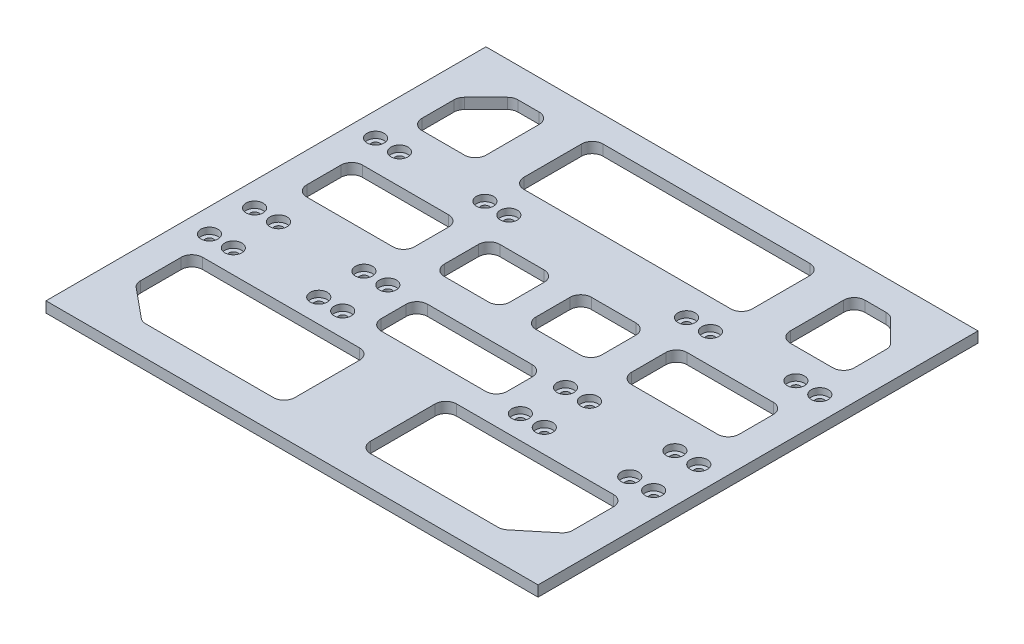
SolidWorks part; units mm, degrees
material "Custom Plastic"
ref_plane "Front Plane" through (0, 0, 0) normal (0, 0, 1) x (1, 0, 0)
ref_plane "Top Plane" through (0, 0, 0) normal (0, 1, 0) x (1, 0, 0)
ref_plane "Right Plane" through (0, 0, 0) normal (1, 0, 0) x (0, 0, -1)
sketch "Sketch1" plane through (0, 0, 0) normal (0, 1, 0) x (1, 0, 0)
  line L1 (-57.5, -51.5) -> (57.5, -51.5)
  line L2 (-57.5, -51.5) -> (-57.5, 51.5)
  line L3 (-57.5, 51.5) -> (57.5, 51.5)
  line L4 (57.5, -51.5) -> (57.5, 51.5)
  line L5 (-57.5, -51.5) -> (57.5, 51.5) construction
  line L6 (-57.5, 51.5) -> (57.5, -51.5) construction
  point P0 (0, 0)
  dimension "D1" = 115
  dimension "D2" = 103
extrude "Boss-Extrude1" add sketch "Sketch1" along normal blind 2.5
sketch "Sketch2" plane through (0, 0, 0) normal (0, -1, 0) x (1, 0, 0)
  line L0 (-57.5, 51.5) -> (57.5, 51.5) construction
  line L1 (-57.5, -51.5) -> (-57.5, 51.5) construction
  line L2 (0, 51.5) -> (0, -51.5) construction
  line L3 (57.5, -51.5) -> (-57.5, -51.5) construction
  line L4 (-46.4, 51.5) -> (-46.4, -51.5) construction
  circle A0 centre (-52, -20.06) radius 1
  circle A1 centre (-52, 8.27) radius 1
  circle A2 centre (-52, 18.84) radius 1
  circle A3 centre (52, -20.06) radius 1
  circle A4 centre (52, 8.27) radius 1
  circle A5 centre (52, 18.84) radius 1
  circle A6 centre (-46.4, 18.84) radius 1
  circle A7 centre (-46.4, -20.06) radius 1
  circle A8 centre (-46.4, 8.27) radius 1
  circle A9 centre (46.4, -20.06) radius 1
  circle A10 centre (46.4, 8.27) radius 1
  circle A11 centre (46.4, 18.84) radius 1
  dimension "D7" = 2
  dimension "D8" = 2
  dimension "D9" = 2
  dimension "D12" = 2
  dimension "D14" = 2
  dimension "D15" = 43.23
  dimension "D16" = 2
  dimension "D1" = 32.66
  dimension "D2" = 43.23
  dimension "D3" = 71.56
  dimension "D4" = 5.5
  dimension "D5" = 5.5
  dimension "D6" = 5.5
  dimension "D10" = 11.1
  dimension "D11" = 32.66
  dimension "D13" = 71.56
extrude "Cut-Extrude1" cut sketch "Sketch2" against normal blind 10
sketch "Sketch3" plane through (-57.5, 0, 0) normal (-1, 0, 0) x (0, 0, 1)
  line L8 (-51.5, 0) -> (51.5, 0)
  line L9 (51.5, 0) -> (51.5, 2.5)
  line L10 (51.5, 2.5) -> (-51.5, 2.5)
  line L11 (-51.5, 2.5) -> (-51.5, 0)
  line L12 (-51.5, 0) -> (51.5, 0)
  line L13 (51.5, 0) -> (51.5, 2.5)
  line L14 (51.5, 2.5) -> (-51.5, 2.5)
  line L15 (-51.5, 2.5) -> (-51.5, 0)
  dimension "D1" = 0
extrude "Boss-Extrude2" add sketch "Sketch3" along normal blind 0.1
sketch "Sketch4" plane through (57.5, 0, 0) normal (1, 0, 0) x (0, 0, -1)
  line L4 (-51.5, 0) -> (51.5, 0)
  line L5 (51.5, 0) -> (51.5, 2.5)
  line L6 (51.5, 2.5) -> (-51.5, 2.5)
  line L7 (-51.5, 2.5) -> (-51.5, 0)
  line L8 (-51.5, 0) -> (51.5, 0)
  line L9 (51.5, 0) -> (51.5, 2.5)
  line L10 (51.5, 2.5) -> (-51.5, 2.5)
  line L11 (-51.5, 2.5) -> (-51.5, 0)
  dimension "D1" = 0
extrude "Boss-Extrude3" add sketch "Sketch4" along normal blind 0.1
sketch "Sketch5" plane through (0, 2.5, 0) normal (0, 1, 0) x (1, 0, 0)
  line L0 (-52, 20.06) -> (52, 20.06) construction
  line L1 (-52, -8.27) -> (52, -8.27) construction
  line L2 (-52, -18.84) -> (52, -18.84) construction
  line L3 (0, 51.5) -> (0, -51.5) construction
  line L4 (57.6, 51.5) -> (-57.6, 51.5) construction
  line L5 (-57.6, -51.5) -> (57.6, -51.5) construction
  circle A0 centre (-26.4, 20.06) radius 1
  circle A1 centre (-26.4, -8.27) radius 1
  circle A2 centre (-26.4, -18.84) radius 1
  circle A3 centre (-20.8, 20.06) radius 1
  circle A4 centre (-20.8, -8.27) radius 1
  circle A5 centre (-20.8, -18.84) radius 1
  circle A6 centre (26.4, -18.84) radius 1
  circle A7 centre (20.8, -18.84) radius 1
  circle A8 centre (26.4, -8.27) radius 1
  circle A9 centre (20.8, -8.27) radius 1
  circle A10 centre (26.4, 20.06) radius 1
  circle A11 centre (20.8, 20.06) radius 1
  dimension "D4" = 2
  dimension "D5" = 2
  dimension "D6" = 2
  dimension "D7" = 2
  dimension "D8" = 2
  dimension "D9" = 2
  dimension "D1" = 31.2
  dimension "D2" = 31.2
  dimension "D3" = 31.2
  dimension "D10" = 5.6
  dimension "D11" = 5.6
  dimension "D12" = 5.6
extrude "Cut-Extrude2" cut sketch "Sketch5" against normal blind 10
sketch "Sketch6" plane through (0, 2.5, 0) normal (0, 1, 0) x (1, 0, 0)
  line L0 (-44.8762, 43.7678) -> (-49.8678, 38.7762)
  line L1 (-50.6, 37.0084) -> (-50.6, 29.5256)
  line L2 (-48.1, 27.0256) -> (-38.1257, 27.0256)
  line L3 (-35.6257, 29.5256) -> (-35.6257, 42)
  line L4 (-38.1257, 44.5) -> (-43.1084, 44.5)
  line L5 (57.6, 51.5) -> (-57.6, 51.5) construction
  line L6 (0, 64.7841) -> (0, -71.4614) construction
  line L7 (-24.2114, 45.5) -> (24.2114, 45.5)
  line L8 (-26.7114, 43) -> (-26.7114, 29.5256)
  line L9 (-24.2114, 27.0256) -> (24.2114, 27.0256)
  line L10 (26.7114, 43) -> (26.7114, 29.5256)
  line L11 (-49.6888, -38.3001) -> (-42.8486, -43.9302)
  line L12 (-48.1, 0.0564) -> (-27.9271, 0.0564)
  line L13 (-50.6, 2.5564) -> (-50.6, 10.569)
  line L14 (-48.1, 13.069) -> (-27.9271, 13.069)
  line L15 (-25.4271, 2.5564) -> (-25.4271, 10.569)
  line L16 (-50.6, 0.0564) -> (-25.4271, 13.069) construction
  line L17 (-50.6, 13.069) -> (-25.4271, 0.0564) construction
  line L18 (-15.9179, 0.0564) -> (-5.5337, 0.0564)
  line L19 (-18.4179, 2.5564) -> (-18.4179, 10.569)
  line L20 (-15.9179, 13.069) -> (-5.5337, 13.069)
  line L21 (-3.0337, 2.5564) -> (-3.0337, 10.569)
  line L22 (-18.4179, 0.0564) -> (-3.0337, 13.069) construction
  line L23 (-18.4179, 13.069) -> (-3.0337, 0.0564) construction
  line L24 (-41.2598, -44.5) -> (-11.3488, -44.5)
  line L25 (-50.6, -36.3699) -> (-50.6, -26.8363)
  line L26 (-48.1, -24.3363) -> (-11.3488, -24.3363)
  line L27 (-8.8488, -42) -> (-8.8488, -26.8363)
  line L28 (-47.0786, -40.4486) -> (-8.8488, -24.3363) construction
  line L29 (-50.6, -24.3363) -> (-8.8488, -44.5) construction
  line L30 (-57.6, -51.5) -> (-57.6, 51.5) construction
  line L32 (-57.6, -51.5) -> (57.6, -51.5) construction
  line L33 (41.2598, -44.5) -> (11.3488, -44.5)
  line L34 (-12.2501, -18.3965) -> (12.2501, -18.3965)
  line L35 (-14.7501, -15.8965) -> (-14.7501, -10.0236)
  line L36 (-12.2501, -7.5236) -> (12.2501, -7.5236)
  line L37 (14.7501, -15.8965) -> (14.7501, -10.0236)
  line L38 (-14.7501, -18.3965) -> (14.7501, -7.5236) construction
  line L39 (-14.7501, -7.5236) -> (14.7501, -18.3965) construction
  line L40 (8.8488, -42) -> (8.8488, -26.8363)
  line L41 (48.1, -24.3363) -> (11.3488, -24.3363)
  line L42 (50.6, -36.3699) -> (50.6, -26.8363)
  line L43 (49.6888, -38.3001) -> (42.8486, -43.9302)
  line L44 (3.0337, 2.5564) -> (3.0337, 10.569)
  line L45 (15.9179, 13.069) -> (5.5337, 13.069)
  line L46 (18.4179, 2.5564) -> (18.4179, 10.569)
  line L47 (15.9179, 0.0564) -> (5.5337, 0.0564)
  line L48 (48.1, 0.0564) -> (27.9271, 0.0564)
  line L49 (50.6, 2.5564) -> (50.6, 10.569)
  line L50 (48.1, 13.069) -> (27.9271, 13.069)
  line L51 (25.4271, 2.5564) -> (25.4271, 10.569)
  line L52 (48.1, 27.0256) -> (38.1257, 27.0256)
  line L53 (50.6, 37.0084) -> (50.6, 29.5256)
  line L54 (44.8762, 43.7678) -> (49.8678, 38.7762)
  line L55 (38.1257, 44.5) -> (43.1084, 44.5)
  line L56 (35.6257, 29.5256) -> (35.6257, 42)
  arc A0 (-49.8678, 38.7762) -> (-50.6, 37.0084) centre (-48.1, 37.0084) ccw
  arc A1 (-44.8762, 43.7678) -> (-43.1084, 44.5) centre (-43.1084, 42) cw
  arc A2 (-42.8486, -43.9302) -> (-41.2598, -44.5) centre (-41.2598, -42) ccw
  arc A3 (-49.6888, -38.3001) -> (-50.6, -36.3699) centre (-48.1, -36.3699) cw
  arc A4 (-50.6, -26.8363) -> (-48.1, -24.3363) centre (-48.1, -26.8363) cw
  arc A5 (-11.3488, -44.5) -> (-8.8488, -42) centre (-11.3488, -42) ccw
  arc A6 (-11.3488, -24.3363) -> (-8.8488, -26.8363) centre (-11.3488, -26.8363) cw
  arc A7 (12.2501, -7.5236) -> (14.7501, -10.0236) centre (12.2501, -10.0236) cw
  arc A8 (12.2501, -18.3965) -> (14.7501, -15.8965) centre (12.2501, -15.8965) ccw
  arc A9 (-12.2501, -18.3965) -> (-14.7501, -15.8965) centre (-12.2501, -15.8965) cw
  arc A10 (-14.7501, -10.0236) -> (-12.2501, -7.5236) centre (-12.2501, -10.0236) cw
  arc A11 (-27.9271, 13.069) -> (-25.4271, 10.569) centre (-27.9271, 10.569) cw
  arc A12 (-27.9271, 0.0564) -> (-25.4271, 2.5564) centre (-27.9271, 2.5564) ccw
  arc A13 (-48.1, 0.0564) -> (-50.6, 2.5564) centre (-48.1, 2.5564) cw
  arc A14 (-50.6, 10.569) -> (-48.1, 13.069) centre (-48.1, 10.569) cw
  arc A15 (24.2114, 27.0256) -> (26.7114, 29.5256) centre (24.2114, 29.5256) ccw
  arc A16 (24.2114, 45.5) -> (26.7114, 43) centre (24.2114, 43) cw
  arc A17 (-5.5337, 13.069) -> (-3.0337, 10.569) centre (-5.5337, 10.569) cw
  arc A18 (-5.5337, 0.0564) -> (-3.0337, 2.5564) centre (-5.5337, 2.5564) ccw
  arc A19 (-15.9179, 0.0564) -> (-18.4179, 2.5564) centre (-15.9179, 2.5564) cw
  arc A20 (-18.4179, 10.569) -> (-15.9179, 13.069) centre (-15.9179, 10.569) cw
  arc A21 (-24.2114, 45.5) -> (-26.7114, 43) centre (-24.2114, 43) ccw
  arc A22 (-26.7114, 29.5256) -> (-24.2114, 27.0256) centre (-24.2114, 29.5256) ccw
  arc A23 (-38.1257, 27.0256) -> (-35.6257, 29.5256) centre (-38.1257, 29.5256) ccw
  arc A24 (-35.6257, 42) -> (-38.1257, 44.5) centre (-38.1257, 42) ccw
  arc A25 (-50.6, 29.5256) -> (-48.1, 27.0256) centre (-48.1, 29.5256) ccw
  arc A26 (42.8486, -43.9302) -> (41.2598, -44.5) centre (41.2598, -42) cw
  arc A27 (11.3488, -44.5) -> (8.8488, -42) centre (11.3488, -42) cw
  arc A28 (11.3488, -24.3363) -> (8.8488, -26.8363) centre (11.3488, -26.8363) ccw
  arc A29 (50.6, -26.8363) -> (48.1, -24.3363) centre (48.1, -26.8363) ccw
  arc A30 (49.6888, -38.3001) -> (50.6, -36.3699) centre (48.1, -36.3699) ccw
  arc A31 (5.5337, 0.0564) -> (3.0337, 2.5564) centre (5.5337, 2.5564) cw
  arc A32 (5.5337, 13.069) -> (3.0337, 10.569) centre (5.5337, 10.569) ccw
  arc A33 (18.4179, 10.569) -> (15.9179, 13.069) centre (15.9179, 10.569) ccw
  arc A34 (15.9179, 0.0564) -> (18.4179, 2.5564) centre (15.9179, 2.5564) ccw
  arc A35 (27.9271, 13.069) -> (25.4271, 10.569) centre (27.9271, 10.569) ccw
  arc A36 (27.9271, 0.0564) -> (25.4271, 2.5564) centre (27.9271, 2.5564) cw
  arc A37 (48.1, 0.0564) -> (50.6, 2.5564) centre (48.1, 2.5564) ccw
  arc A38 (50.6, 10.569) -> (48.1, 13.069) centre (48.1, 10.569) ccw
  arc A39 (38.1257, 27.0256) -> (35.6257, 29.5256) centre (38.1257, 29.5256) cw
  arc A40 (50.6, 29.5256) -> (48.1, 27.0256) centre (48.1, 29.5256) cw
  arc A41 (49.8678, 38.7762) -> (50.6, 37.0084) centre (48.1, 37.0084) cw
  arc A42 (44.8762, 43.7678) -> (43.1084, 44.5) centre (43.1084, 42) ccw
  arc A43 (35.6257, 42) -> (38.1257, 44.5) centre (38.1257, 42) cw
  point P14 (0, 45.5)
  point P15 (-38.0136, 6.5627)
  point P20 (-10.7258, 6.5627)
  point P26 (-31.1437, -33.7327)
  point P36 (0, -12.9601)
  dimension "D6" = 2.5
  dimension "D1" = 7
  dimension "D2" = 7
  dimension "D3" = 7
  dimension "D4" = 7
  dimension "D5" = 7
extrude "Cut-Extrude3" cut sketch "Sketch6" against normal blind 10
sketch "Sketch7" plane through (0, 2.5, 0) normal (0, 1, 0) x (1, 0, 0)
  line L0 (0, 56.9722) -> (0, -76.8259) construction
  circle A0 centre (-52, 20.06) radius 2
  circle A1 centre (-46.4, 20.06) radius 2
  circle A2 centre (-26.4, 20.06) radius 2
  circle A3 centre (-20.8, 20.06) radius 2
  circle A4 centre (-52, -8.27) radius 2
  circle A5 centre (-46.4, -8.27) radius 2
  circle A6 centre (-52, -18.84) radius 2
  circle A7 centre (-46.4, -18.84) radius 2
  circle A8 centre (-26.4, -18.84) radius 2
  circle A9 centre (-20.8, -18.84) radius 2
  circle A10 centre (-20.8, -8.27) radius 2
  circle A11 centre (-26.4, -8.27) radius 2
  circle A12 centre (20.8, -18.84) radius 2
  circle A13 centre (26.4, -18.84) radius 2
  circle A14 centre (20.8, -8.27) radius 2
  circle A15 centre (26.4, -8.27) radius 2
  circle A16 centre (46.4, -18.84) radius 2
  circle A17 centre (52, -18.84) radius 2
  circle A18 centre (46.4, -8.27) radius 2
  circle A19 centre (52, -8.27) radius 2
  circle A20 centre (20.8, 20.06) radius 2
  circle A21 centre (26.4, 20.06) radius 2
  circle A22 centre (52, 20.06) radius 2
  circle A23 centre (46.4, 20.06) radius 2
  dimension "D1" = 4
  dimension "D2" = 4
  dimension "D3" = 4
  dimension "D4" = 4
  dimension "D5" = 4
  dimension "D6" = 4
  dimension "D7" = 4
  dimension "D8" = 4
  dimension "D9" = 4
  dimension "D10" = 4
  dimension "D11" = 4
  dimension "D12" = 4
extrude "Cut-Extrude4" cut sketch "Sketch7" against normal blind 1.5
